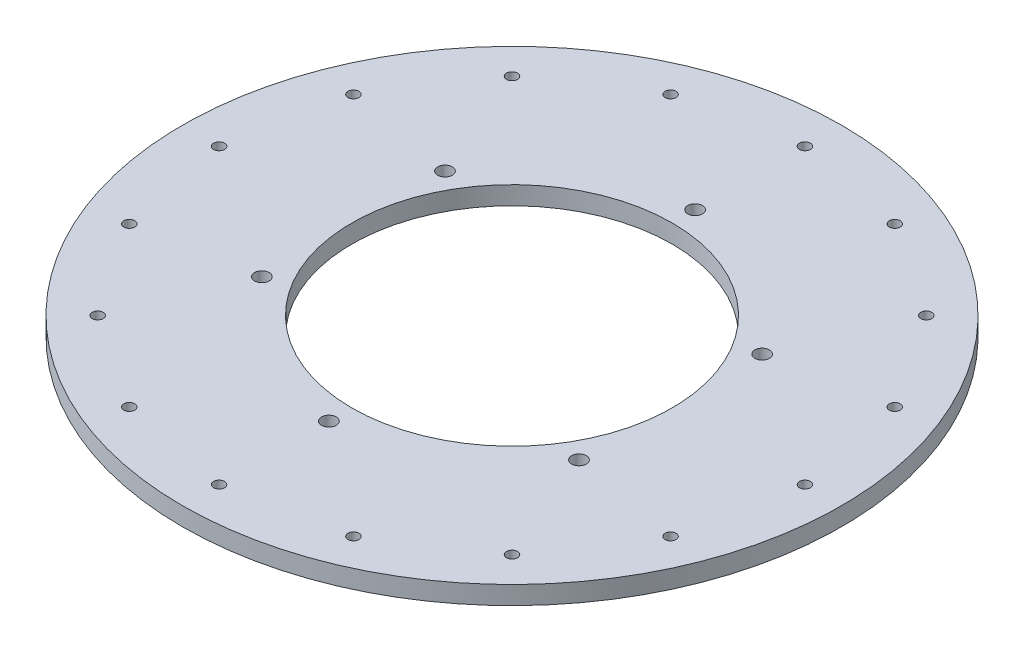
SolidWorks part; units mm, degrees
ref_plane "Front Plane" through (0, 0, 0) normal (0, 0, 1) x (1, 0, 0)
ref_plane "Top Plane" through (0, 0, 0) normal (0, 1, 0) x (1, 0, 0)
ref_plane "Right Plane" through (0, 0, 0) normal (1, 0, 0) x (0, 0, -1)
sketch "Sketch1" plane through (0, 0, 0) normal (0, 1, 0) x (1, 0, 0)
  line L1 (0, 100) -> (-86.6025, 50) construction
  line L2 (-86.6025, 50) -> (-86.6025, -50) construction
  line L3 (-86.6025, -50) -> (0, -100) construction
  line L4 (0, -100) -> (86.6025, -50) construction
  line L5 (86.6025, -50) -> (86.6025, 50) construction
  line L6 (86.6025, 50) -> (0, 100) construction
  circle A0 centre (0, 0) radius 87.5
  circle A1 centre (0, 0) radius 180
  circle A8 centre (0, 160) radius 3
  circle A9 centre (0, 0) radius 115 construction
  circle A43 centre (61.2293, 147.8207) radius 3
  circle A44 centre (113.1371, 113.1371) radius 3
  circle A45 centre (147.8207, 61.2293) radius 3
  circle A46 centre (160, 0) radius 3
  circle A47 centre (147.8207, -61.2293) radius 3
  circle A48 centre (113.1371, -113.1371) radius 3
  circle A49 centre (61.2293, -147.8207) radius 3
  circle A50 centre (0, -160) radius 3
  circle A51 centre (-61.2293, -147.8207) radius 3
  circle A52 centre (-113.1371, -113.1371) radius 3
  circle A53 centre (-147.8207, -61.2293) radius 3
  circle A54 centre (-160, 0) radius 3
  circle A55 centre (-147.8207, 61.2293) radius 3
  circle A56 centre (-113.1371, 113.1371) radius 3
  circle A57 centre (-61.2293, 147.8207) radius 3
  circle A73 centre (0, 0) radius 86.6025 construction
  circle A74 centre (0, 100) radius 4
  circle A75 centre (86.6025, 50) radius 4
  circle A76 centre (86.6025, -50) radius 4
  circle A77 centre (0, -100) radius 4
  circle A78 centre (-86.6025, -50) radius 4
  circle A79 centre (-86.6025, 50) radius 4
  point P19 (0, 0)
  point P33 (0, 0)
  point P51 (0, 0)
  point P55 (0, 0)
  point P56 (0, 0)
  point P61 (0, 0)
  dimension "D1" = 175
  dimension "D3" = 200
  dimension "D5" = 6
  dimension "D2" = 360
  dimension "D7" = 230
  dimension "D4" = 8
  dimension "D6" = 160
  dimension "D8" = 16
extrude "Boss-Extrude1" add sketch "Sketch1" along normal blind 10
